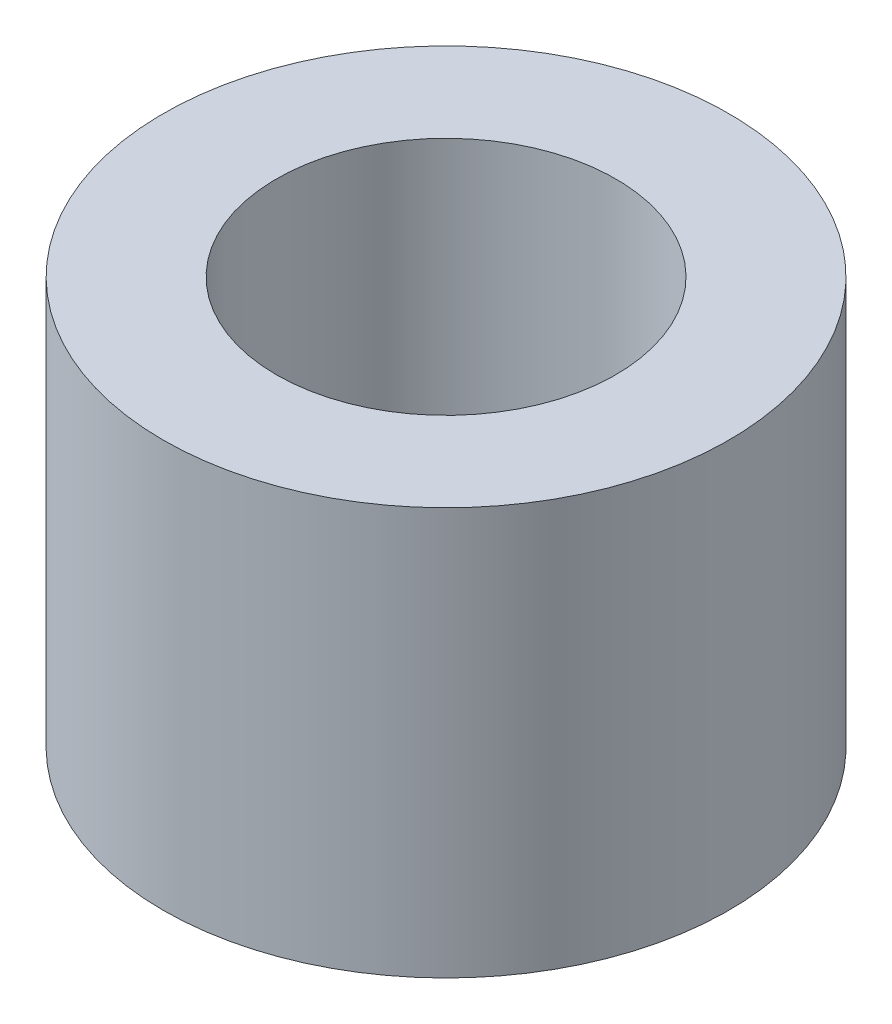
SolidWorks part; units mm, degrees
ref_plane "Plan de face" through (0, 0, 0) normal (0, 0, 1) x (1, 0, 0)
ref_plane "Plan de dessus" through (0, 0, 0) normal (0, 1, 0) x (1, 0, 0)
ref_plane "Plan de droite" through (0, 0, 0) normal (1, 0, 0) x (0, 0, -1)
sketch "Esquisse1" plane through (0, 0, 0) normal (0, 1, 0) x (1, 0, 0)
  circle A0 centre (0, 0) radius 1.25
  circle A1 centre (0, 0) radius 0.75
  dimension "D1" = 1.5
  dimension "D2" = 2.5
extrude "Extrusion1" add sketch "Esquisse1" along normal blind 1.8
